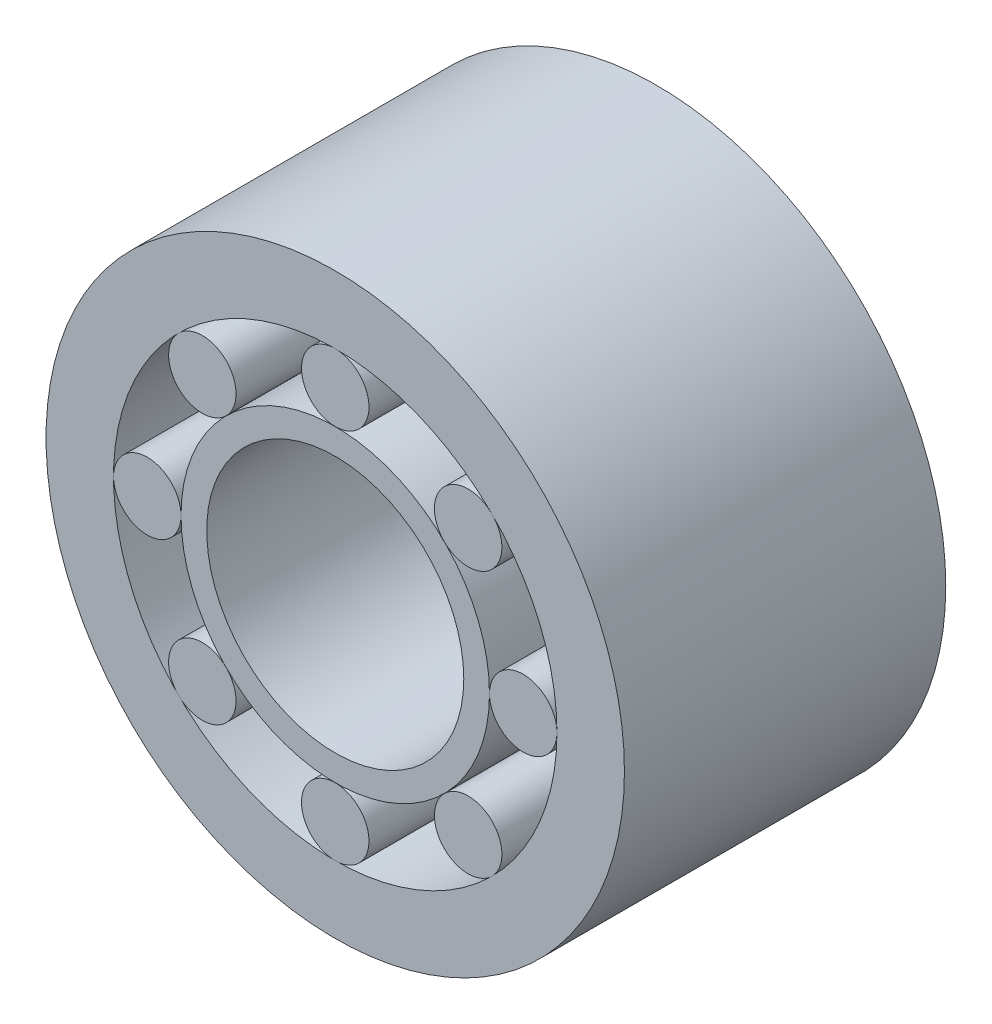
SolidWorks part; units mm, degrees
ref_plane "前视基准面" through (0, 0, 0) normal (0, 0, 1) x (1, 0, 0)
ref_plane "上视基准面" through (0, 0, 0) normal (0, 1, 0) x (1, 0, 0)
ref_plane "右视基准面" through (0, 0, 0) normal (1, 0, 0) x (0, 0, -1)
sketch "草图1" plane through (0, 0, 0) normal (0, 0, 1) x (1, 0, 0)
  circle A0 centre (0, 0) radius 90
  circle A1 centre (0, 0) radius 40
  dimension "D1" = 180
extrude "凸台-拉伸1" add sketch "草图1" along normal blind 100
sketch "草图2" plane through (0, 0, 0) normal (0, 0, 1) x (1, 0, 0)
  circle A0 centre (0, 0) radius 48
  circle A1 centre (0, 0) radius 69
  dimension "D1" = 138
  dimension "D2" = 96
extrude "切除-拉伸2" cut sketch "草图2" along normal through all
sketch "草图3" plane through (0, 0, 0) normal (1, 0, 0) x (0, 0, -1)
  line L1 (-104.8328, 58.5) -> (7.9032, 58.5) construction
  line L2 (-70, 58.5) -> (-70, 69)
  line L3 (-70, 69) -> (-100, 69)
  line L4 (-100, 90) -> (-100, -90) construction
  line L5 (-100, 69) -> (-100, 58.5)
  line L6 (-100, 58.5) -> (-70, 58.5)
  line L7 (-65, 58.5) -> (-35, 58.5)
  line L8 (-30.0043, 58.5) -> (-0.0043, 58.5)
  line L9 (-65, 58.5) -> (-65, 69)
  line L10 (-65, 69) -> (-35, 69)
  line L11 (-35, 69) -> (-35, 58.5)
  line L16 (-35.0529, 58.5) -> (-35.0529, 69)
  line L20 (-30.0043, 58.5) -> (-30.0043, 69)
  line L21 (-30.0043, 69) -> (-0.0043, 69)
  line L22 (-0.0043, 69) -> (-0.0043, 58.5)
  dimension "D6" = 30
  dimension "D7" = 30
revolve "旋转1" add sketch "草图3" angle 360 about L6
pattern_circular "阵列(圆周)4" count 8 over 360 about axis through (0, 0, 0) along (0, 0, 1) of bodies 111 110 109
sketch "草图4" plane through (0, 0, 0) normal (1, 0, 0) x (0, 0, -1)
  line L0 (-70, 53) -> (-65, 53)
  line L1 (-70, 48) -> (-70, 69) construction
  line L2 (-65, 69) -> (-65, 48) construction
  line L3 (-65, 53) -> (-65, 48)
  line L4 (-65, 48) -> (-70, 48)
  line L5 (-70, 48) -> (-70, 53)
  line L12 (-35.0529, 53) -> (-30.0043, 53)
  line L13 (-35.0529, 48) -> (-35.0529, 69) construction
  line L14 (-30.0043, 69) -> (-30.0043, 48) construction
  line L15 (-30.0043, 53) -> (-30.0043, 48)
  line L16 (-30.0043, 48) -> (-35.0529, 48)
  line L17 (-35.0529, 48) -> (-35.0529, 53)
  line L18 (-111.2696, 0) -> (17.0457, 0) construction
  dimension "D1" = 5
  dimension "D2" = 5
revolve "旋转4" add sketch "草图4" angle 360 about L18
